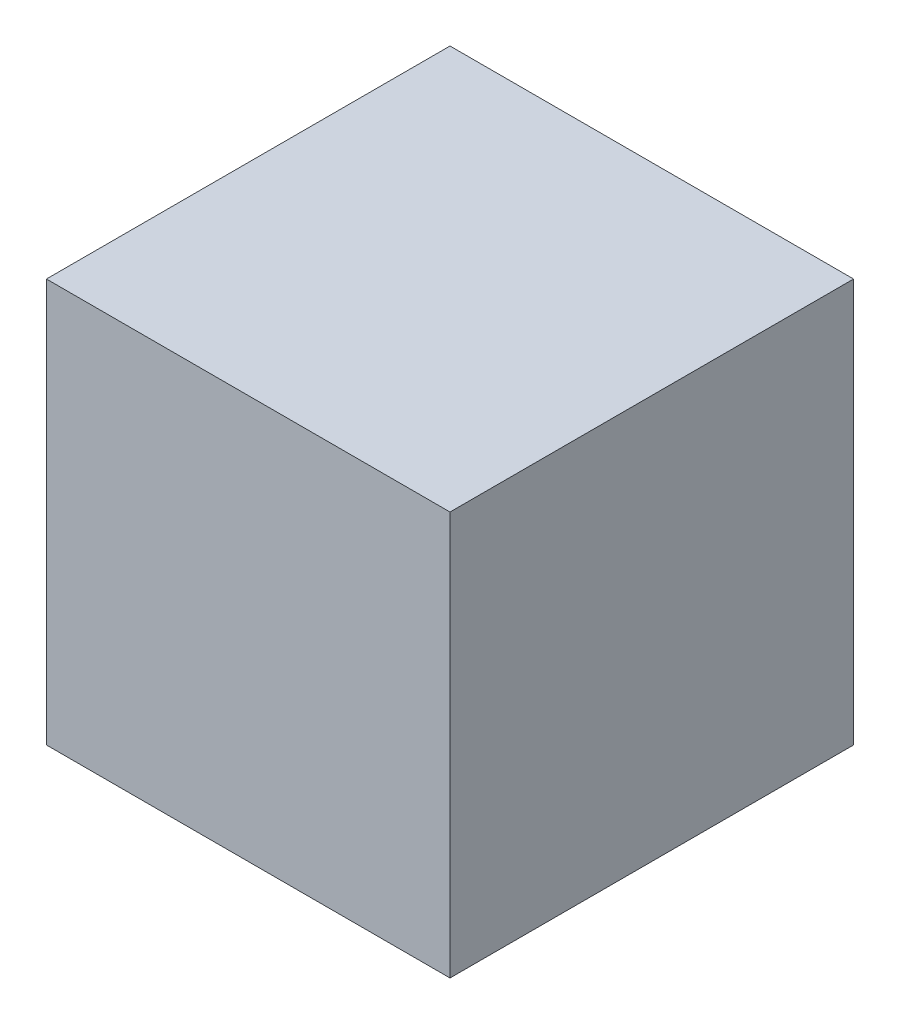
SolidWorks part; units mm, degrees
ref_plane "Płaszczyzna przednia" through (0, 0, 0) normal (0, 0, 1) x (1, 0, 0)
ref_plane "Płaszczyzna górna" through (0, 0, 0) normal (0, 1, 0) x (1, 0, 0)
ref_plane "Płaszczyzna prawa" through (0, 0, 0) normal (1, 0, 0) x (0, 0, -1)
sketch "Szkic1" plane through (0, 0, 0) normal (0, 0, 1) x (1, 0, 0)
  line L1 (-17.5, -17.5) -> (17.5, -17.5)
  line L2 (-17.5, -17.5) -> (-17.5, 17.5)
  line L3 (-17.5, 17.5) -> (17.5, 17.5)
  line L4 (17.5, -17.5) -> (17.5, 17.5)
  line L5 (-17.5, -17.5) -> (17.5, 17.5) construction
  line L6 (-17.5, 17.5) -> (17.5, -17.5) construction
  point P0 (0, 0)
  dimension "D1" = 35
  dimension "D2" = 35
extrude "Dodanie-wyciągnięcie1" add sketch "Szkic1" along normal blind 35
